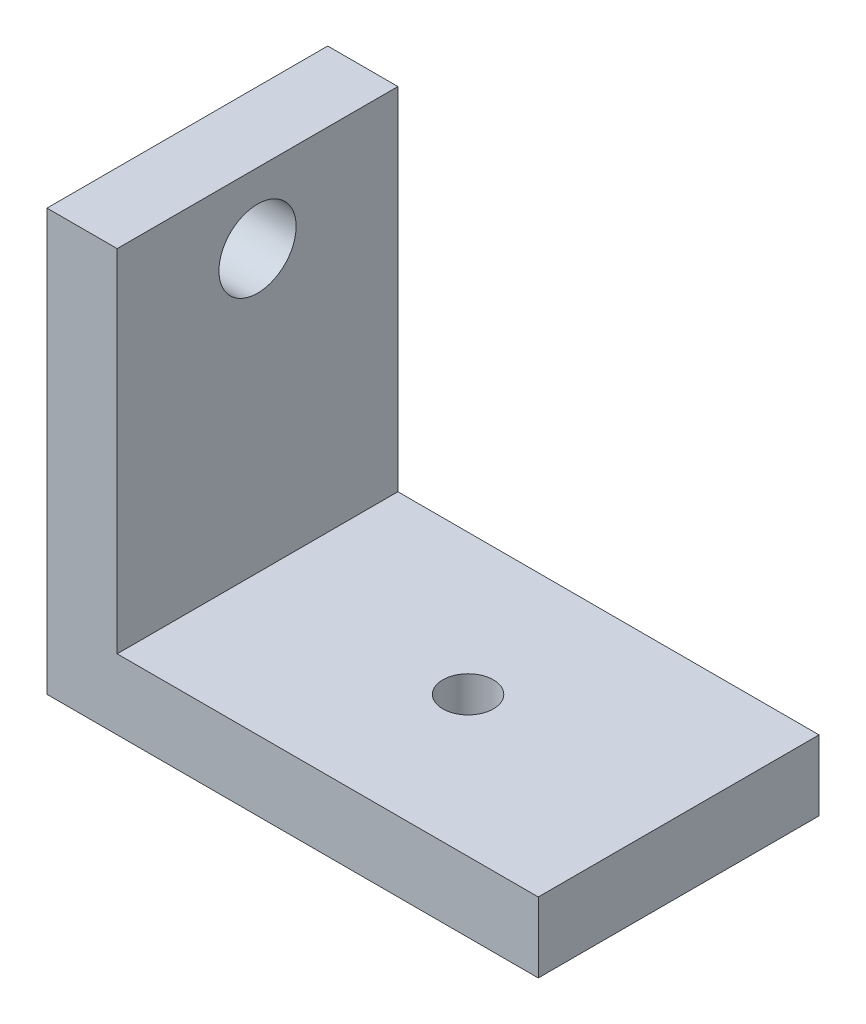
SolidWorks part; units mm, degrees
ref_plane "前视基准面" through (0, 0, 0) normal (0, 0, 1) x (1, 0, 0)
ref_plane "上视基准面" through (0, 0, 0) normal (0, 1, 0) x (1, 0, 0)
ref_plane "右视基准面" through (0, 0, 0) normal (1, 0, 0) x (0, 0, -1)
other "Configuration Table"
sketch "草图5" plane through (0, 0, 0) normal (1, 0, 0) x (0, 0, -1)
  line L1 (-10, 15) -> (10, 15)
  line L2 (-10, 15) -> (-10, -15)
  line L3 (-10, -15) -> (10, -15)
  line L4 (10, 15) -> (10, -15)
  circle A0 centre (0, 10) radius 2.75
extrude "凸台-拉伸1" add sketch "草图5" along normal blind 5
sketch "草图6" plane through (5, 0, 0) normal (1, 0, 0) x (0, 0, -1)
  line L0 (-10, 15) -> (-10, -15) construction
  line L1 (10, -15) -> (-10, -15)
  line L2 (10, -15) -> (10, -10)
  line L3 (10, -10) -> (-10, -10)
  line L4 (-10, -15) -> (-10, -10)
extrude "凸台-拉伸2" add sketch "草图6" along normal blind 30 contours L3 L4 L1 L2
sketch "草图7" plane through (0, -10, 0) normal (0, 1, 0) x (1, 0, 0)
  circle A0 centre (20, 0) radius 1.8
extrude "切除-拉伸1" cut sketch "草图7" against normal through all
